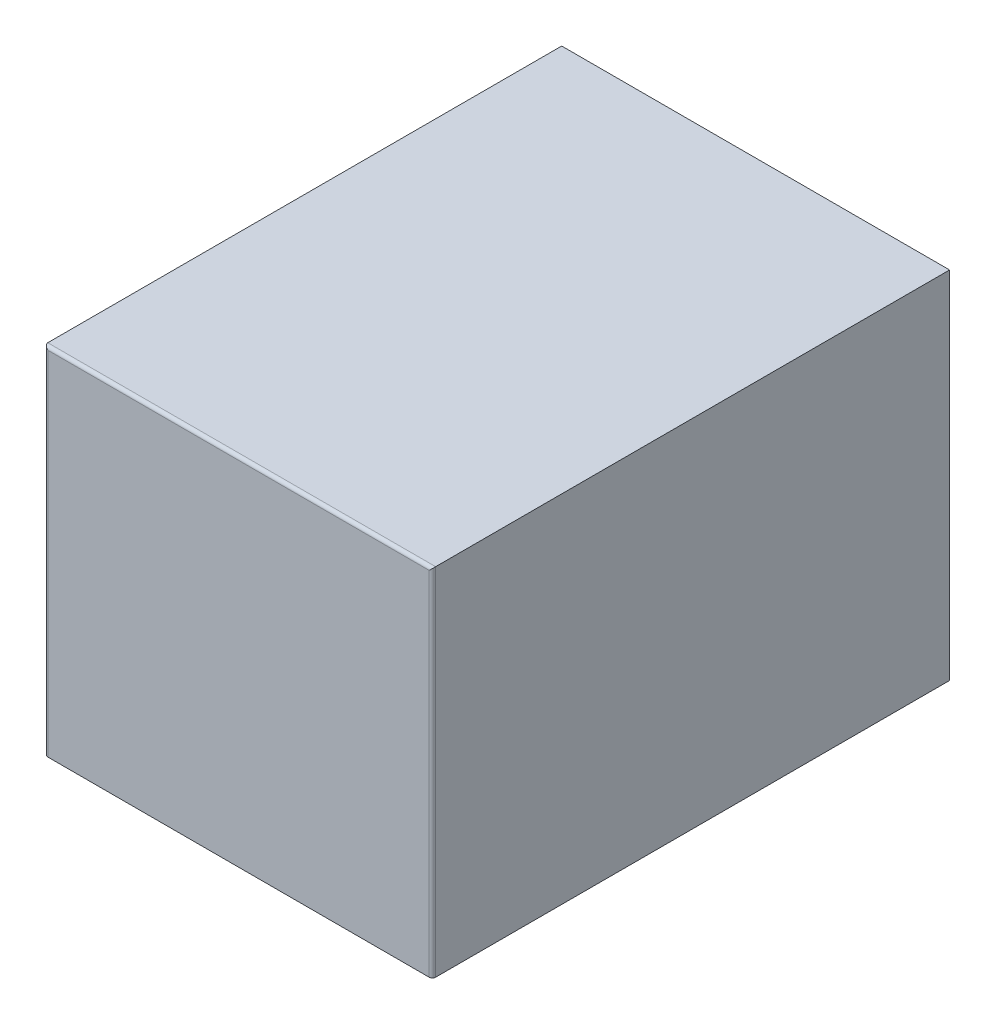
SolidWorks part; units mm, degrees
material "1060 Alloy"
ref_plane "Front Plane" through (0, 0, 0) normal (0, 0, 1) x (1, 0, 0)
ref_plane "Top Plane" through (0, 0, 0) normal (0, 1, 0) x (1, 0, 0)
ref_plane "Right Plane" through (0, 0, 0) normal (1, 0, 0) x (0, 0, -1)
sketch "Sketch1" plane through (0, 0, 0) normal (0, 1, 0) x (1, 0, 0)
  line L1 (-6, 8) -> (6, 8)
  line L2 (-6, 8) -> (-6, -8)
  line L3 (-6, -8) -> (6, -8)
  line L4 (6, 8) -> (6, -8)
  line L5 (-6, 8) -> (6, -8) construction
  line L6 (-6, -8) -> (6, 8) construction
  point P0 (0, 0)
  dimension "D1" = 12
  dimension "D2" = 16
extrude "Boss-Extrude1" add sketch "Sketch1" along normal blind 11
sketch "Sketch4" plane through (0, 0, -8) normal (0, 0, -1) x (-1, 0, 0)
  line L0 (-4.9422, 1.3046) -> (5.2058, 1.3046)
  line L1 (5.2058, 1.3046) -> (5.2058, 7.4329)
  line L2 (5.2058, 7.4329) -> (3.4046, 9.8491)
  line L3 (3.4046, 9.8491) -> (-3.0092, 9.8491)
  line L4 (-3.0092, 9.8491) -> (-4.9422, 7.4329)
  line L5 (-4.9422, 7.4329) -> (-4.9422, 1.3046)
extrude "Cut-Extrude1" cut sketch "Sketch4" against normal blind 11
fillet "Fillet1" radius 0.1 3 edges at (-6, 5.5, 8) (6, 5.5, 8) (0, 11, 8)
sketch "Sketch5" plane through (0, 0, 3) normal (0, 0, -1) x (-1, 0, 0)
  line L1 (-3.141, 7.282) -> (3.4046, 7.282)
  line L2 (-3.141, 7.282) -> (-3.141, 3.4979)
  line L3 (-3.141, 3.4979) -> (3.4046, 3.4979)
  line L4 (3.4046, 7.282) -> (3.4046, 3.4979)
  line L5 (-3.141, 7.282) -> (3.4046, 3.4979) construction
  line L6 (-3.141, 3.4979) -> (3.4046, 7.282) construction
  point P0 (0.1318, 5.39)
extrude "Boss-Extrude2" add sketch "Sketch5" along normal blind 10
